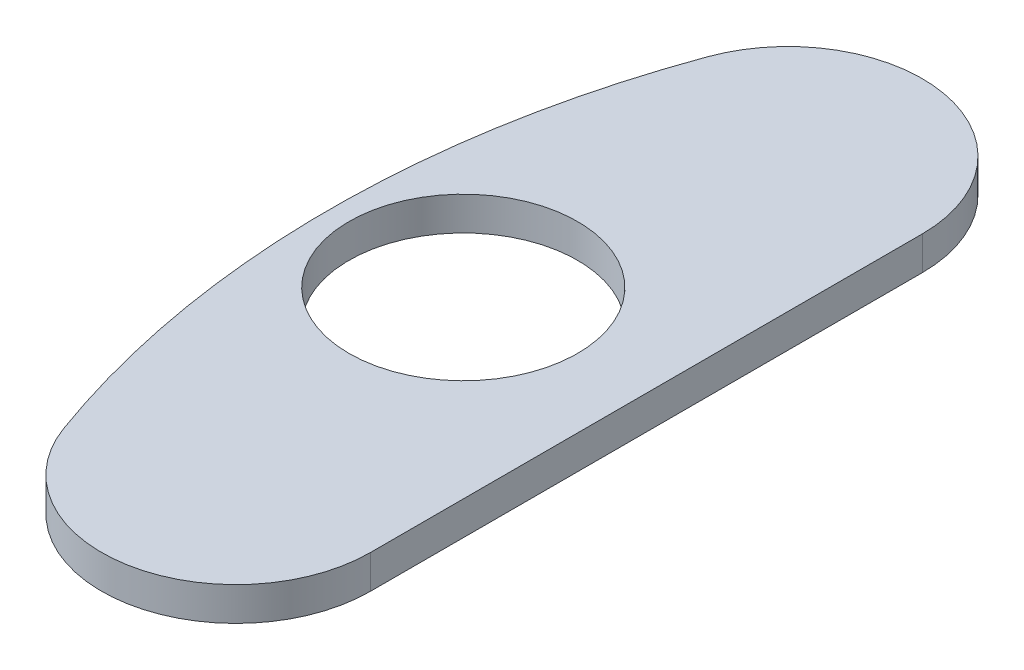
SolidWorks part; units mm, degrees
material "Plain Carbon Steel"
ref_plane "Front Plane" through (0, 0, 0) normal (0, 0, 1) x (1, 0, 0)
ref_plane "Top Plane" through (0, 0, 0) normal (0, 1, 0) x (1, 0, 0)
ref_plane "Right Plane" through (0, 0, 0) normal (1, 0, 0) x (0, 0, -1)
sketch "Sketch1" plane through (0, 0, 0) normal (0, 1, 0) x (1, 0, 0)
  line L0 (-71.6046, 26.0619) -> (0, 0) construction
  line L1 (-71.6046, -26.0619) -> (0, 0) construction
  line L2 (-58.9046, 26.0619) -> (-58.9046, -26.0619)
  arc A0 (-65.6375, 23.8901) -> (-65.6375, -23.8901) centre (0, 0) ccw construction
  arc A1 (-77.5716, 28.2338) -> (-77.5716, -28.2338) centre (0, 0) ccw construction
  arc A2 (-71.6046, 26.0619) -> (-71.6046, -26.0619) centre (0, 0) ccw construction
  arc A3 (-77.5716, 28.2338) -> (-65.6375, 23.8901) centre (-71.6046, 26.0619) cw construction
  arc A4 (-77.5716, -28.2338) -> (-65.6375, -23.8901) centre (-71.6046, -26.0619) ccw construction
  arc A6 (-83.5387, 30.4056) -> (-83.5387, -30.4056) centre (0, 0) ccw
  arc A7 (-83.5387, 30.4056) -> (-58.9046, 26.0619) centre (-71.6046, 26.0619) cw
  arc A8 (-83.5387, -30.4056) -> (-58.9046, -26.0619) centre (-71.6046, -26.0619) ccw
  circle A9 centre (-76.2, 0) radius 10.795
  point P8 (-76.2, 0)
  point P15 (0, 0)
  dimension "D1" = 76.2
  dimension "D3" = 12.7
  dimension "D4" = 88.9
  dimension "D5" = 21.59
  dimension "D2" = 40
extrude "Boss-Extrude2" add sketch "Sketch1" along normal blind 3.175
